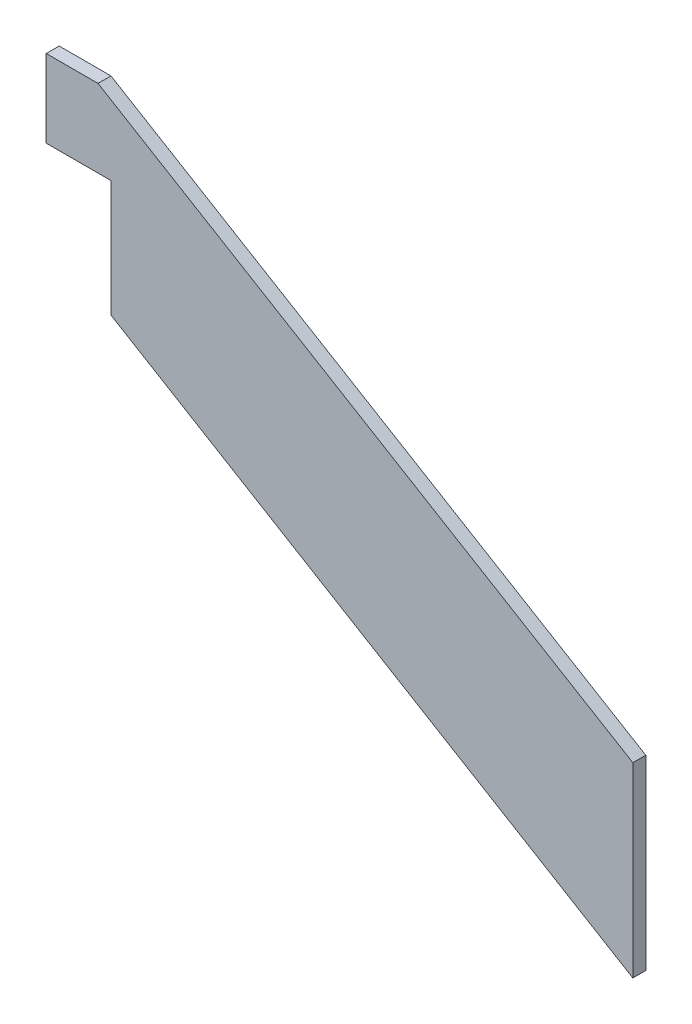
SolidWorks part; units mm, degrees
ref_plane "Plan de face" through (0, 0, 0) normal (0, 0, 1) x (1, 0, 0)
ref_plane "Plan de dessus" through (0, 0, 0) normal (0, 1, 0) x (1, 0, 0)
ref_plane "Plan de droite" through (0, 0, 0) normal (1, 0, 0) x (0, 0, -1)
sketch "Esquisse1" plane through (0, 0, 0) normal (0, 0, 1) x (1, 0, 0)
  line L0 (0, 0) -> (-40.3022, 24.1813)
  line L1 (-40.3022, 24.1813) -> (-40.3022, 33.1813)
  line L2 (-40.3022, 33.1813) -> (-45.3022, 33.1813)
  line L3 (-45.3022, 33.1813) -> (-45.3022, 39.1813)
  line L4 (-45.3022, 39.1813) -> (-41.3022, 39.1813)
  line L5 (-41.3022, 39.1813) -> (0, 14.4)
  line L6 (0, 14.4) -> (0, 0)
  dimension "D1" = 47
  dimension "D2" = 5
  dimension "D3" = 6
  dimension "D4" = 4
  dimension "D5" = 9
  dimension "D6" = 14.4
extrude "Boss.-Extru.1" add sketch "Esquisse1" along normal blind 1
